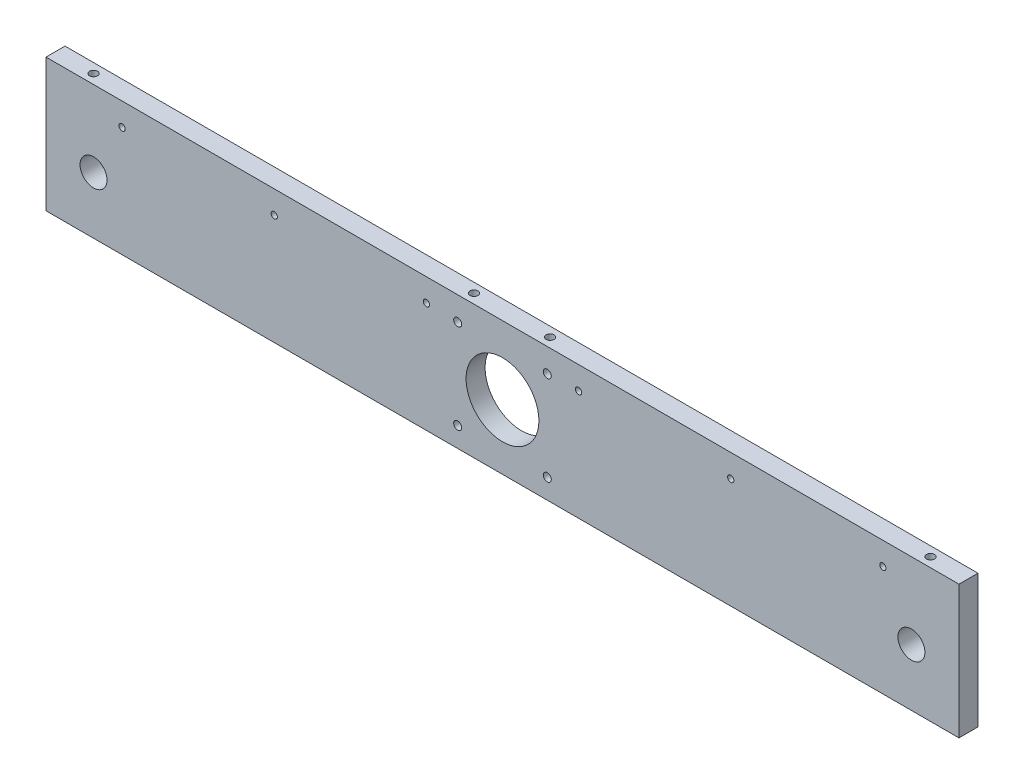
SolidWorks part; units mm, degrees
ref_plane "Front Plane" through (0, 0, 0) normal (0, 0, 1) x (1, 0, 0)
ref_plane "Top Plane" through (0, 0, 0) normal (0, 1, 0) x (1, 0, 0)
ref_plane "Right Plane" through (0, 0, 0) normal (1, 0, 0) x (0, 0, -1)
sketch "Sketch1" plane through (0, 0, 0) normal (0, 0, 1) x (1, 0, 0)
  line L0 (0, 35) -> (0, -35) construction
  line L1 (-240, 35) -> (240, 35)
  line L2 (-240, 35) -> (-240, -35)
  line L3 (-240, -35) -> (240, -35)
  line L4 (240, 35) -> (240, -35)
  line L5 (-240, 35) -> (240, -35) construction
  line L6 (-240, -35) -> (240, 35) construction
  line L7 (0, -1) -> (0, 18.15) construction
  line L8 (0, 18.15) -> (0, -1) construction
  line L9 (0, -1) -> (-19.15, -1) construction
  circle A0 centre (0, -1) radius 19.15
  circle A1 centre (-23.55, -24.55) radius 2.1
  circle A2 centre (23.55, -24.55) radius 2.1
  circle A3 centre (23.55, 22.55) radius 2.1
  circle A4 centre (-23.55, 22.55) radius 2.1
  circle A5 centre (-215, -5) radius 7.1
  circle A6 centre (215, -5) radius 7.1
  point P0 (0, 0)
  point P34 (-138.5559, -1)
  point P35 (0, 0)
  dimension "D3" = 4.2
  dimension "D4" = 38.3
  dimension "D7" = 36
  dimension "D8" = 14.2
  dimension "D10" = 25
  dimension "D1" = 480
  dimension "D2" = 70
  dimension "D9" = 40
  dimension "D5" = 2
  dimension "D6" = 2
extrude "Boss-Extrude1" add sketch "Sketch1" along normal blind 10
hole_wizard "M5 Tapped Hole1" positions "Sketch2" profile "Sketch3" tap size "M5" standard "ISO"
sketch "Sketch2" plane through (0, 35, 0) normal (0, 1, 0) x (1, 0, 0)
  line L0 (-240, -5) -> (240, -5) construction
  line L1 (-240, -10) -> (-240, 0) construction
  line L2 (240, -10) -> (240, 0) construction
  line L4 (0, 1.5912) -> (0, -10) construction
  line L5 (240, -10) -> (-240, -10) construction
  point P13 (-220, -5)
  point P15 (-20, -5)
  point P18 (20, -5)
  point P19 (220, -5)
  dimension "D1" = 20
  dimension "D2" = 20
sketch "Sketch3" plane through (220, 35, 5) normal (1, 0, 0) x (0, 0, 1)
  line L0 (0, 0) -> (0, 13.6618)
  line L1 (0, 13.6618) -> (2.1, 12.4)
  line L2 (2.1, 12.4) -> (2.1, 0)
  line L5 (2.1, 0) -> (0, 0)
  line L10 (0, 13.6618) -> (-2.1, 12.4) construction
  line L11 (0, -6.35) -> (0, 107.95) construction
  dimension "Tap Drill Dia." = 4.2
  dimension "Tap Drill Depth" = 12.4
  dimension "Drill Angle" = 118
cosmetic thread "Hole Thread1" parameters "D1"=10, "D2"=5
cosmetic thread "Hole Thread2" parameters "D1"=10, "D2"=5
cosmetic thread "Hole Thread3" parameters "D1"=10, "D2"=5
cosmetic thread "Hole Thread4" parameters "D1"=10, "D2"=5
hole_wizard "M5 Tapped Hole2" positions "Sketch4" profile "Sketch5" tap size "M5" standard "ISO"
sketch "Sketch4" plane through (0, -35, 0) normal (0, -1, 0) x (-1, 0, 0)
  line L0 (0, -10) -> (0, 0) construction
  line L1 (240, -10) -> (-240, -10) construction
  line L4 (240, -5) -> (-240, -5) construction
  line L5 (240, -10) -> (240, 0) construction
  line L6 (-240, -10) -> (-240, 0) construction
  point P16 (220, -5)
  point P19 (-220, -5)
  dimension "D1" = 20
sketch "Sketch5" plane through (220, -35, 5) normal (1, 0, 0) x (0, 0, -1)
  line L0 (0, 0) -> (0, 13.6618)
  line L1 (0, 13.6618) -> (2.1, 12.4)
  line L2 (2.1, 12.4) -> (2.1, 0)
  line L5 (2.1, 0) -> (0, 0)
  line L10 (0, 13.6618) -> (-2.1, 12.4) construction
  line L11 (0, -6.35) -> (0, 107.95) construction
  dimension "Tap Drill Dia." = 4.2
  dimension "Tap Drill Depth" = 12.4
  dimension "Drill Angle" = 118
cosmetic thread "Hole Thread5" parameters "D1"=10, "D2"=5
cosmetic thread "Hole Thread6" parameters "D1"=10, "D2"=5
hole_wizard "Ø3.3 (3.3) Diameter Hole1" positions "Sketch6" profile "Sketch7" hole size "Ø3.3" standard "ISO" end condition through all
sketch "Sketch6" plane through (0, 0, 10) normal (0, 0, 1) x (1, 0, 0)
  line L0 (-240, 35) -> (-240, -35) construction
  line L1 (240, 35) -> (-240, 35) construction
  point P0 (-200, 23)
  point P10 (-120, 23)
  point P11 (-40, 23)
  point P12 (40, 23)
  point P13 (120, 23)
  point P14 (200, 23)
  dimension "D1" = 40
  dimension "D2" = 12
  dimension "D3" = 6
sketch "Sketch7" plane through (-200, 23, 10) normal (1, 0, 0) x (0, -1, 0)
  line L0 (0, 0) -> (0, 10)
  line L1 (0, 10) -> (1.65, 10)
  line L2 (1.65, 10) -> (1.65, 0)
  line L5 (1.65, 0) -> (0, 0)
  line L11 (0, -6.35) -> (0, 107.95) construction
  dimension "Thru Hole Dia." = 3.3
  dimension "Thru Hole Depth" = 10
